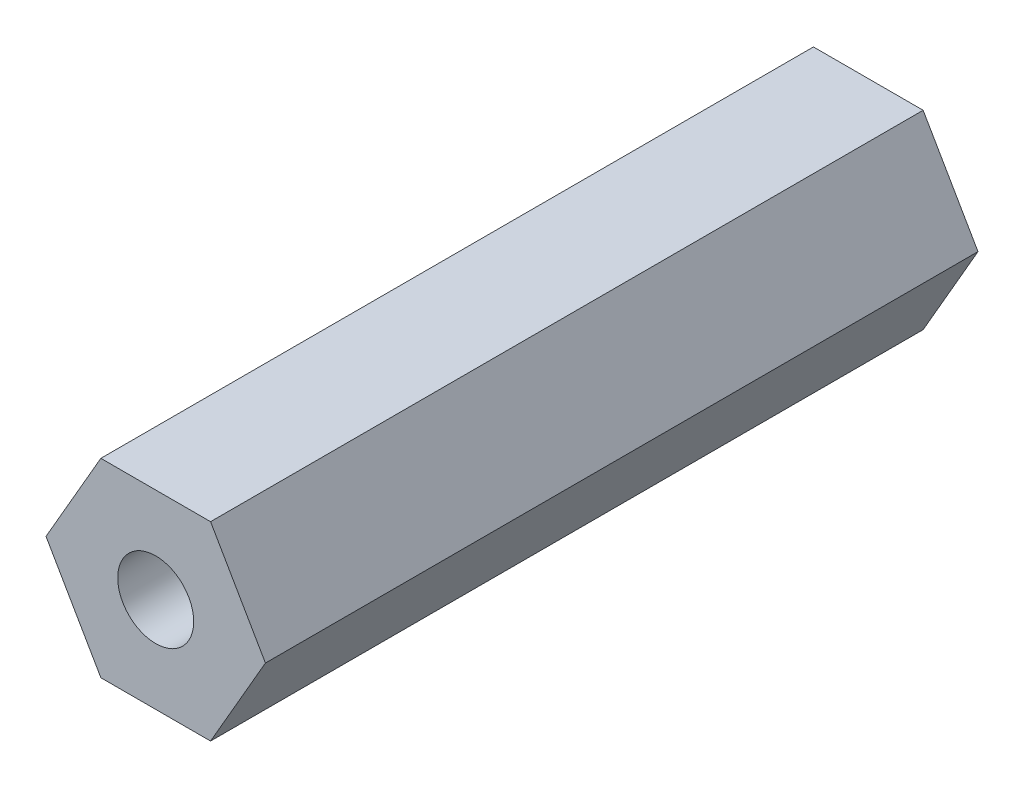
SolidWorks part; units mm, degrees
material "6061 合金"
ref_plane "前视基准面" through (0, 0, 0) normal (0, 0, 1) x (1, 0, 0)
ref_plane "上视基准面" through (0, 0, 0) normal (0, 1, 0) x (1, 0, 0)
ref_plane "右视基准面" through (0, 0, 0) normal (1, 0, 0) x (0, 0, -1)
sketch "草图1" plane through (0, 0, 0) normal (0, 0, 1) x (1, 0, 0)
  line L1 (1.1547, 2) -> (-1.1547, 2)
  line L2 (-1.1547, 2) -> (-2.3094, 0)
  line L3 (-2.3094, 0) -> (-1.1547, -2)
  line L4 (-1.1547, -2) -> (1.1547, -2)
  line L5 (1.1547, -2) -> (2.3094, 0)
  line L6 (2.3094, 0) -> (1.1547, 2)
  circle A0 centre (0, 0) radius 2 construction
  dimension "D1" = 4
extrude "凸台-拉伸1" add sketch "草图1" along normal blind 15
hole_wizard "M2 螺纹孔1" positions "草图2" profile "草图3" tap size "M2" standard "GB" end condition through all
sketch "草图2" plane through (0, 0, 15) normal (0, 0, 1) x (1, 0, 0)
  point P0 (0, 0)
sketch "草图3" plane through (0, 0, 15) normal (1, 0, 0) x (0, -1, 0)
  line L0 (0, 0) -> (0, 15)
  line L1 (0, 15) -> (0.8, 15)
  line L2 (0.8, 15) -> (0.8, 0)
  line L5 (0.8, 0) -> (0, 0)
  line L11 (0, -6.35) -> (0, 107.95) construction
  dimension "通孔螺纹孔钻头直径" = 1.6
  dimension "通孔螺纹孔钻头深度" = 15
cosmetic thread "孔螺蚊线1"
